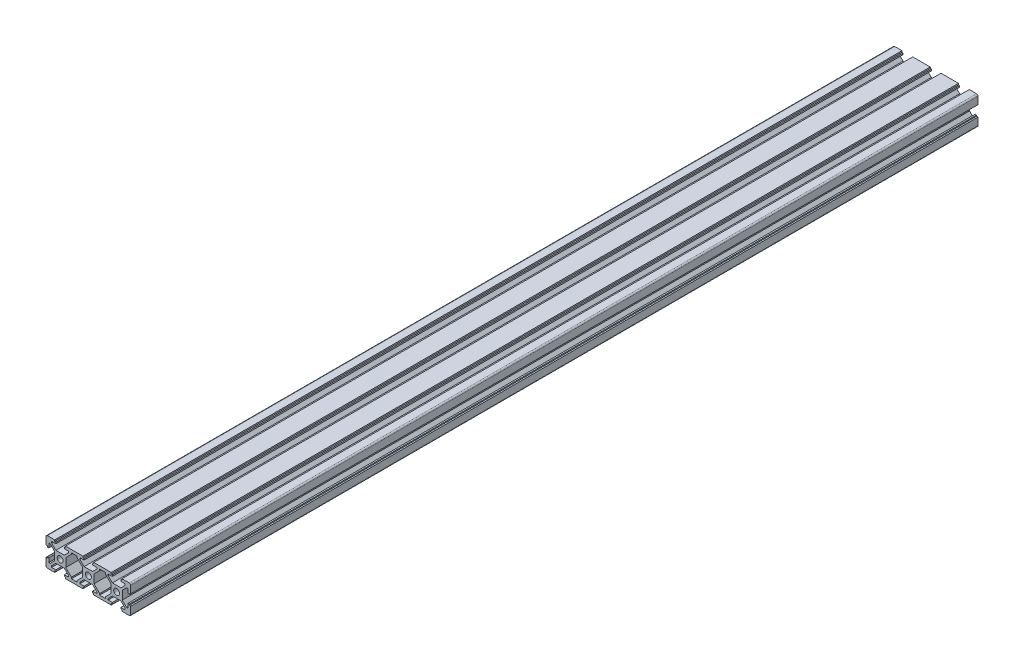
SolidWorks part; units mm, degrees
material "6061 合金"
ref_plane "前视基准面" through (0, 0, 0) normal (0, 0, 1) x (1, 0, 0)
ref_plane "上视基准面" through (0, 0, 0) normal (0, 1, 0) x (1, 0, 0)
ref_plane "右视基准面" through (0, 0, 0) normal (1, 0, 0) x (0, 0, -1)
sketch "草图1" plane through (0, 0, 0) normal (0, 0, 1) x (1, 0, 0)
  line L0 (-32.2486, -0.2298) -> (-32.2486, -1.031)
  line L1 (-32.2486, -1.031) -> (-33.25, -1.031)
  line L2 (-33.25, -1.031) -> (-33.25, -6.2384)
  line L3 (-32.2438, -7.2255) -> (-27.0786, -7.2255)
  line L4 (-27.0786, -7.2255) -> (-27.0786, -6.2241)
  line L5 (-27.0786, -6.2241) -> (-26.2774, -6.2241)
  line L6 (-26.2774, -6.2241) -> (-26.2774, -5.2127)
  line L7 (-26.2774, -5.2127) -> (-29.273, -5.2127)
  line L8 (-29.273, -5.2127) -> (-29.273, -4.2115)
  line L9 (-29.273, -4.2115) -> (-26.2796, -1.2254)
  line L10 (-26.2796, -1.2254) -> (-20.249, -1.2254)
  line L14 (-20.249, -1.2254) -> (-17.2556, -4.2115)
  line L15 (-17.2556, -4.2115) -> (-17.2556, -5.2127)
  line L16 (-17.2556, -5.2127) -> (-20.2513, -5.2127)
  line L17 (-20.2513, -5.2127) -> (-20.2513, -6.2241)
  line L18 (-20.2513, -6.2241) -> (-19.4501, -6.2241)
  line L19 (-19.4501, -6.2241) -> (-19.4501, -7.2255)
  line L20 (-19.4501, -7.2255) -> (-7.0642, -7.2255)
  line L21 (-7.0642, -7.2255) -> (-7.0642, -6.2241)
  line L22 (-7.0642, -6.2241) -> (-6.2631, -6.2241)
  line L23 (-6.2631, -6.2241) -> (-6.2631, -5.2127)
  line L24 (-6.2631, -5.2127) -> (-9.2587, -5.2127)
  line L25 (-9.2587, -5.2127) -> (-9.2587, -4.2115)
  line L26 (-9.2587, -4.2115) -> (-6.2653, -1.2254)
  line L27 (-6.2653, -1.2254) -> (-0.2347, -1.2254)
  line L31 (-0.2347, -1.2254) -> (2.7587, -4.2115)
  line L32 (2.7587, -4.2115) -> (2.7587, -5.2127)
  line L33 (2.7587, -5.2127) -> (-0.2369, -5.2127)
  line L34 (-0.2369, -5.2127) -> (-0.2369, -6.2241)
  line L35 (-0.2369, -6.2241) -> (0.5642, -6.2241)
  line L36 (0.5642, -6.2241) -> (0.5642, -7.2255)
  line L37 (0.5642, -7.2255) -> (12.9455, -7.2255)
  line L38 (12.9455, -7.2255) -> (12.9455, -6.2191)
  line L39 (12.9455, -6.2191) -> (13.7512, -6.2191)
  line L40 (13.7512, -6.2191) -> (13.7512, -5.2127)
  line L41 (13.7512, -5.2127) -> (10.7556, -5.2127)
  line L42 (10.7556, -5.2127) -> (10.7556, -4.2115)
  line L43 (10.7556, -4.2115) -> (13.749, -1.2254)
  line L44 (13.749, -1.2254) -> (19.7796, -1.2254)
  line L48 (19.7796, -1.2254) -> (22.773, -4.2115)
  line L49 (22.773, -4.2115) -> (22.773, -5.2127)
  line L50 (22.773, -5.2127) -> (19.7728, -5.2127)
  line L51 (19.7728, -5.2127) -> (19.7728, -6.2191)
  line L52 (19.7728, -6.2191) -> (20.5739, -6.2191)
  line L53 (20.5739, -6.2191) -> (20.5739, -7.2255)
  line L54 (20.5739, -7.2255) -> (25.7438, -7.2255)
  line L55 (26.75, -6.2384) -> (26.75, -1.031)
  line L56 (26.75, -1.031) -> (25.7485, -1.031)
  line L57 (25.7485, -1.031) -> (25.7485, -0.2298)
  line L58 (25.7485, -0.2298) -> (24.7613, -0.2298)
  line L59 (24.7613, -0.2298) -> (24.7613, -3.2342)
  line L60 (24.7613, -3.2342) -> (23.7599, -3.2342)
  line L61 (23.7599, -3.2342) -> (20.7701, -0.2372)
  line L65 (20.7701, -0.2372) -> (20.7701, 5.7861)
  line L66 (20.7701, 5.7861) -> (23.7599, 8.7832)
  line L67 (23.7599, 8.7832) -> (24.7613, 8.7832)
  line L68 (24.7613, 8.7832) -> (24.7613, 5.7788)
  line L69 (24.7613, 5.7788) -> (25.7485, 5.7788)
  line L70 (25.7485, 5.7788) -> (25.7485, 6.5799)
  line L71 (25.7485, 6.5799) -> (26.75, 6.5799)
  line L72 (26.75, 6.5799) -> (26.75, 11.7682)
  line L73 (25.7438, 12.7745) -> (20.5739, 12.7745)
  line L74 (20.5739, 12.7745) -> (20.5739, 11.7681)
  line L75 (20.5739, 11.7681) -> (19.7728, 11.7681)
  line L76 (19.7728, 11.7681) -> (19.7728, 10.7617)
  line L77 (19.7728, 10.7617) -> (22.773, 10.7617)
  line L78 (22.773, 10.7617) -> (22.773, 9.7604)
  line L79 (22.773, 9.7604) -> (19.7796, 6.7743)
  line L83 (19.7796, 6.7743) -> (13.749, 6.7743)
  line L84 (13.749, 6.7743) -> (10.7556, 9.7604)
  line L85 (10.7556, 9.7604) -> (10.7556, 10.7617)
  line L86 (10.7556, 10.7617) -> (13.7466, 10.7617)
  line L87 (13.7466, 10.7617) -> (13.7466, 11.7681)
  line L88 (13.7466, 11.7681) -> (12.9455, 11.7681)
  line L89 (12.9455, 11.7681) -> (12.9455, 12.7745)
  line L90 (12.9455, 12.7745) -> (0.5642, 12.7745)
  line L91 (0.5642, 12.7745) -> (0.5642, 11.773)
  line L92 (0.5642, 11.773) -> (-0.2369, 11.773)
  line L93 (-0.2369, 11.773) -> (-0.2369, 10.7617)
  line L94 (-0.2369, 10.7617) -> (2.7587, 10.7617)
  line L95 (2.7587, 10.7617) -> (2.7587, 9.7604)
  line L96 (2.7587, 9.7604) -> (-0.2347, 6.7743)
  line L100 (-0.2347, 6.7743) -> (-6.2653, 6.7743)
  line L101 (-6.2653, 6.7743) -> (-9.2587, 9.7604)
  line L102 (-9.2587, 9.7604) -> (-9.2587, 10.7617)
  line L103 (-9.2587, 10.7617) -> (-6.2631, 10.7617)
  line L104 (-6.2631, 10.7617) -> (-6.2631, 11.773)
  line L105 (-6.2631, 11.773) -> (-7.0642, 11.773)
  line L106 (-7.0642, 11.773) -> (-7.0642, 12.7745)
  line L107 (-7.0642, 12.7745) -> (-19.4501, 12.7745)
  line L108 (-19.4501, 12.7745) -> (-19.4501, 11.773)
  line L109 (-19.4501, 11.773) -> (-20.2513, 11.773)
  line L110 (-20.2513, 11.773) -> (-20.2513, 10.7617)
  line L111 (-20.2513, 10.7617) -> (-17.2556, 10.7617)
  line L112 (-17.2556, 10.7617) -> (-17.2556, 9.7604)
  line L113 (-17.2556, 9.7604) -> (-20.249, 6.7743)
  line L117 (-20.249, 6.7743) -> (-26.2796, 6.7743)
  line L118 (-26.2796, 6.7743) -> (-29.273, 9.7604)
  line L119 (-29.273, 9.7604) -> (-29.273, 10.7617)
  line L120 (-29.273, 10.7617) -> (-26.2774, 10.7617)
  line L121 (-26.2774, 10.7617) -> (-26.2774, 11.773)
  line L122 (-26.2774, 11.773) -> (-27.0786, 11.773)
  line L123 (-27.0786, 11.773) -> (-27.0786, 12.7745)
  line L124 (-27.0786, 12.7745) -> (-32.2438, 12.7745)
  line L125 (-33.25, 11.7682) -> (-33.25, 6.5608)
  line L126 (-33.25, 6.5608) -> (-32.2486, 6.5608)
  line L127 (-32.2486, 6.5608) -> (-32.2486, 5.7596)
  line L128 (-32.2486, 5.7596) -> (-31.2613, 5.7596)
  line L129 (-31.2613, 5.7596) -> (-31.2613, 8.764)
  line L130 (-31.2613, 8.764) -> (-30.2599, 8.764)
  line L131 (-30.2599, 8.764) -> (-27.2701, 5.767)
  line L135 (-27.2701, 5.767) -> (-27.2701, -0.2372)
  line L136 (-27.2701, -0.2372) -> (-30.2599, -3.2342)
  line L137 (-30.2599, -3.2342) -> (-31.2613, -3.2342)
  line L138 (-31.2613, -3.2342) -> (-31.2613, -0.2298)
  line L139 (-31.2613, -0.2298) -> (-32.2486, -0.2298)
  line L147 (-19.2585, 5.7861) -> (-19.2585, -0.2372)
  line L150 (-19.2585, -0.2372) -> (-15.2673, -4.2381)
  line L151 (-15.2673, -4.2381) -> (-15.2673, -5.2223)
  line L152 (-15.2673, -5.2223) -> (-11.247, -5.2223)
  line L153 (-11.247, -5.2223) -> (-11.247, -4.2381)
  line L154 (-11.247, -4.2381) -> (-7.2558, -0.2372)
  line L155 (-7.2558, -0.2372) -> (-7.2558, 2.7745)
  line L156 (-7.2558, 2.7745) -> (-7.2558, 5.7861)
  line L157 (-7.2558, 5.7861) -> (-11.247, 9.787)
  line L158 (-11.247, 9.787) -> (-11.247, 10.7712)
  line L159 (-11.247, 10.7712) -> (-15.2673, 10.7712)
  line L160 (-15.2673, 10.7712) -> (-15.2673, 9.787)
  line L161 (-15.2673, 9.787) -> (-19.2585, 5.7861)
  line L162 (4.747, -5.2223) -> (8.7673, -5.2223)
  line L163 (8.7673, -5.2223) -> (8.7673, -4.2381)
  line L164 (8.7673, -4.2381) -> (12.7585, -0.2372)
  line L165 (12.7585, -0.2372) -> (12.7585, 2.7745)
  line L166 (12.7585, 2.7745) -> (12.7585, 5.7861)
  line L167 (12.7585, 5.7861) -> (8.7673, 9.787)
  line L168 (8.7673, 9.787) -> (8.7673, 10.7712)
  line L169 (8.7673, 10.7712) -> (4.747, 10.7712)
  line L170 (4.747, 10.7712) -> (4.747, 9.787)
  line L171 (4.747, 9.787) -> (0.7558, 5.7861)
  line L172 (0.7558, 5.7861) -> (0.7558, 2.7745)
  line L173 (0.7558, 2.7745) -> (0.7558, -0.2372)
  line L174 (0.7558, -0.2372) -> (4.747, -4.2381)
  line L175 (4.747, -4.2381) -> (4.747, -5.2223)
  line L176 (-23.25, 2.7745) -> (-23.25, 12.5158) construction
  line L177 (-23.25, 2.7745) -> (-33.2945, 2.7745) construction
  line L178 (-23.25, 2.7745) -> (-23.25, -7.2784) construction
  line L179 (-23.25, 2.7745) -> (-17.6462, 2.7745) construction
  line L180 (-3.25, 2.7745) -> (-3.25, 12.9074) construction
  line L181 (-3.25, 2.7745) -> (-3.25, -7.2598) construction
  line L182 (-3.25, 2.7745) -> (-8.8035, 2.7745) construction
  line L183 (-3.25, 2.7745) -> (2.4087, 2.7745) construction
  line L184 (16.75, 2.7745) -> (16.75, 12.9038) construction
  line L185 (16.75, 2.7745) -> (26.8187, 2.7745) construction
  line L186 (16.75, 2.7745) -> (16.75, -7.3953) construction
  line L187 (16.75, 2.7745) -> (10.7407, 2.7745) construction
  circle A0 centre (-3.25, 2.7745) radius 2.103
  circle A1 centre (-23.25, 2.7745) radius 2.103
  circle A2 centre (16.75, 2.7745) radius 2.103
  arc A3 (-33.25, -6.2384) -> (-32.2438, -7.2255) centre (-32.2487, -6.2241) ccw
  arc A4 (25.7438, -7.2255) -> (26.75, -6.2384) centre (25.7487, -6.2241) ccw
  arc A5 (26.75, 11.7682) -> (25.7438, 12.7745) centre (25.7486, 11.773) ccw
  arc A6 (-32.2438, 12.7745) -> (-33.25, 11.7682) centre (-32.2486, 11.773) ccw
  point P197 (-29.6612, 12.7745)
  dimension "D1" = 60
  dimension "D2" = 20
  dimension "D3" = 20
  dimension "D4" = 20
  dimension "D5" = 10
  dimension "D6" = 10
  dimension "D7" = 10
  dimension "D8" = 10
extrude "凸台-拉伸1" add sketch "草图1" along normal blind 600
